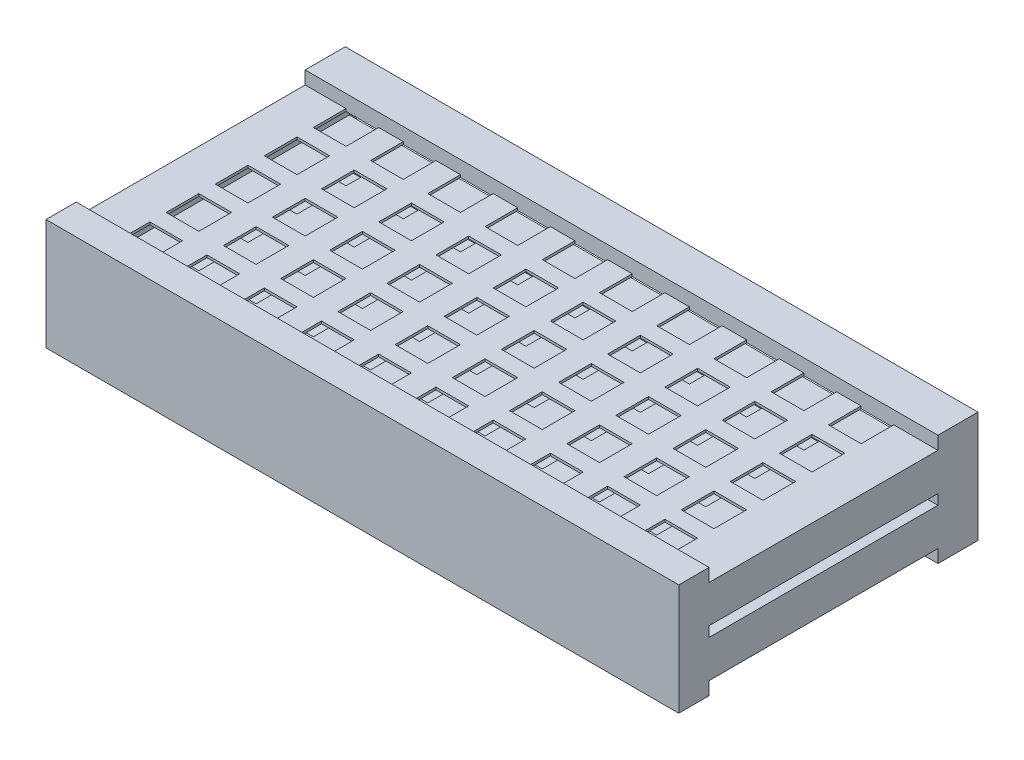
SolidWorks part; units mm, degrees
material "ABS"
ref_plane "Płaszczyzna przednia" through (0, 0, 0) normal (0, 0, 1) x (1, 0, 0)
ref_plane "Płaszczyzna górna" through (0, 0, 0) normal (0, 1, 0) x (1, 0, 0)
ref_plane "Płaszczyzna prawa" through (0, 0, 0) normal (1, 0, 0) x (0, 0, -1)
sketch "Szkic1" plane through (0, 0, 0) normal (0, 0, 1) x (1, 0, 0)
  line L15 (186, 34.1) -> (-188, 34.1)
  line L16 (186, 34.1) -> (186, -18.9)
  line L17 (186, -18.9) -> (-188, -18.9)
  line L18 (-188, 34.1) -> (-188, -18.9)
  point P0 (0, 0)
  dimension "D3" = 374
  dimension "D6" = 53
extrude "Dodanie-wyciągnięcie1" add sketch "Szkic1" along normal blind 177 contours L17 L18 L15 L16
sketch "Szkic5" plane through (0, -18.9, 0) normal (0, -1, 0) x (1, 0, 0)
  line L0 (186, 0) -> (-188, 0) construction
  line L1 (165.5, 48.5) -> (145.5, 48.5)
  line L2 (186, 177) -> (186, 0) construction
  line L3 (165.5, 48.5) -> (165.5, 68.5)
  line L4 (165.5, 68.5) -> (145.5, 68.5)
  line L5 (165.5, 18.5) -> (145.5, 18.5)
  line L6 (165.5, 18.5) -> (165.5, 38.5)
  line L7 (165.5, 38.5) -> (145.5, 38.5)
  line L8 (145.5, 18.5) -> (145.5, 38.5)
  line L9 (145.5, 48.5) -> (145.5, 68.5)
  line L10 (165.5, 78.5) -> (145.5, 78.5)
  line L11 (165.5, 78.5) -> (165.5, 98.5)
  line L12 (165.5, 98.5) -> (145.5, 98.5)
  line L13 (145.5, 78.5) -> (145.5, 98.5)
  line L14 (165.5, 108.5) -> (145.5, 108.5)
  line L15 (165.5, 108.5) -> (165.5, 128.5)
  line L16 (165.5, 128.5) -> (145.5, 128.5)
  line L17 (145.5, 108.5) -> (145.5, 128.5)
  line L18 (165.5, 138.5) -> (145.5, 138.5)
  line L19 (165.5, 138.5) -> (165.5, 158.5)
  line L20 (165.5, 158.5) -> (145.5, 158.5)
  line L21 (145.5, 138.5) -> (145.5, 158.5)
  line L22 (130.5, 48.5) -> (110.5, 48.5)
  line L23 (130.5, 48.5) -> (130.5, 68.5)
  line L24 (130.5, 68.5) -> (110.5, 68.5)
  line L25 (130.5, 18.5) -> (110.5, 18.5)
  line L26 (130.5, 18.5) -> (130.5, 38.5)
  line L27 (130.5, 38.5) -> (110.5, 38.5)
  line L28 (110.5, 18.5) -> (110.5, 38.5)
  line L29 (110.5, 48.5) -> (110.5, 68.5)
  line L30 (130.5, 78.5) -> (110.5, 78.5)
  line L31 (130.5, 78.5) -> (130.5, 98.5)
  line L32 (130.5, 98.5) -> (110.5, 98.5)
  line L33 (110.5, 78.5) -> (110.5, 98.5)
  line L34 (130.5, 108.5) -> (110.5, 108.5)
  line L35 (130.5, 108.5) -> (130.5, 128.5)
  line L36 (130.5, 128.5) -> (110.5, 128.5)
  line L37 (110.5, 108.5) -> (110.5, 128.5)
  line L38 (130.5, 138.5) -> (110.5, 138.5)
  line L39 (130.5, 138.5) -> (130.5, 158.5)
  line L40 (130.5, 158.5) -> (110.5, 158.5)
  line L41 (110.5, 138.5) -> (110.5, 158.5)
  line L42 (95.5, 48.5) -> (75.5, 48.5)
  line L43 (95.5, 48.5) -> (95.5, 68.5)
  line L44 (95.5, 68.5) -> (75.5, 68.5)
  line L45 (95.5, 18.5) -> (75.5, 18.5)
  line L46 (95.5, 18.5) -> (95.5, 38.5)
  line L47 (95.5, 38.5) -> (75.5, 38.5)
  line L48 (75.5, 18.5) -> (75.5, 38.5)
  line L49 (75.5, 48.5) -> (75.5, 68.5)
  line L50 (95.5, 78.5) -> (75.5, 78.5)
  line L51 (95.5, 78.5) -> (95.5, 98.5)
  line L52 (95.5, 98.5) -> (75.5, 98.5)
  line L53 (75.5, 78.5) -> (75.5, 98.5)
  line L54 (95.5, 108.5) -> (75.5, 108.5)
  line L55 (95.5, 108.5) -> (95.5, 128.5)
  line L56 (95.5, 128.5) -> (75.5, 128.5)
  line L57 (75.5, 108.5) -> (75.5, 128.5)
  line L58 (95.5, 138.5) -> (75.5, 138.5)
  line L59 (95.5, 138.5) -> (95.5, 158.5)
  line L60 (95.5, 158.5) -> (75.5, 158.5)
  line L61 (75.5, 138.5) -> (75.5, 158.5)
  line L62 (60.5, 48.5) -> (40.5, 48.5)
  line L63 (60.5, 48.5) -> (60.5, 68.5)
  line L64 (60.5, 68.5) -> (40.5, 68.5)
  line L65 (60.5, 18.5) -> (40.5, 18.5)
  line L66 (60.5, 18.5) -> (60.5, 38.5)
  line L67 (60.5, 38.5) -> (40.5, 38.5)
  line L68 (40.5, 18.5) -> (40.5, 38.5)
  line L69 (40.5, 48.5) -> (40.5, 68.5)
  line L70 (60.5, 78.5) -> (40.5, 78.5)
  line L71 (60.5, 78.5) -> (60.5, 98.5)
  line L72 (60.5, 98.5) -> (40.5, 98.5)
  line L73 (40.5, 78.5) -> (40.5, 98.5)
  line L74 (60.5, 108.5) -> (40.5, 108.5)
  line L75 (60.5, 108.5) -> (60.5, 128.5)
  line L76 (60.5, 128.5) -> (40.5, 128.5)
  line L77 (40.5, 108.5) -> (40.5, 128.5)
  line L78 (60.5, 138.5) -> (40.5, 138.5)
  line L79 (60.5, 138.5) -> (60.5, 158.5)
  line L80 (60.5, 158.5) -> (40.5, 158.5)
  line L81 (40.5, 138.5) -> (40.5, 158.5)
  line L82 (25.5, 48.5) -> (5.5, 48.5)
  line L83 (25.5, 48.5) -> (25.5, 68.5)
  line L84 (25.5, 68.5) -> (5.5, 68.5)
  line L85 (25.5, 18.5) -> (5.5, 18.5)
  line L86 (25.5, 18.5) -> (25.5, 38.5)
  line L87 (25.5, 38.5) -> (5.5, 38.5)
  line L88 (5.5, 18.5) -> (5.5, 38.5)
  line L89 (5.5, 48.5) -> (5.5, 68.5)
  line L90 (25.5, 78.5) -> (5.5, 78.5)
  line L91 (25.5, 78.5) -> (25.5, 98.5)
  line L92 (25.5, 98.5) -> (5.5, 98.5)
  line L93 (5.5, 78.5) -> (5.5, 98.5)
  line L94 (25.5, 108.5) -> (5.5, 108.5)
  line L95 (25.5, 108.5) -> (25.5, 128.5)
  line L96 (25.5, 128.5) -> (5.5, 128.5)
  line L97 (5.5, 108.5) -> (5.5, 128.5)
  line L98 (25.5, 138.5) -> (5.5, 138.5)
  line L99 (25.5, 138.5) -> (25.5, 158.5)
  line L100 (25.5, 158.5) -> (5.5, 158.5)
  line L101 (5.5, 138.5) -> (5.5, 158.5)
  line L102 (-9.5, 48.5) -> (-29.5, 48.5)
  line L103 (-9.5, 48.5) -> (-9.5, 68.5)
  line L104 (-9.5, 68.5) -> (-29.5, 68.5)
  line L105 (-9.5, 18.5) -> (-29.5, 18.5)
  line L106 (-9.5, 18.5) -> (-9.5, 38.5)
  line L107 (-9.5, 38.5) -> (-29.5, 38.5)
  line L108 (-29.5, 18.5) -> (-29.5, 38.5)
  line L109 (-29.5, 48.5) -> (-29.5, 68.5)
  line L110 (-9.5, 78.5) -> (-29.5, 78.5)
  line L111 (-9.5, 78.5) -> (-9.5, 98.5)
  line L112 (-9.5, 98.5) -> (-29.5, 98.5)
  line L113 (-29.5, 78.5) -> (-29.5, 98.5)
  line L114 (-9.5, 108.5) -> (-29.5, 108.5)
  line L115 (-9.5, 108.5) -> (-9.5, 128.5)
  line L116 (-9.5, 128.5) -> (-29.5, 128.5)
  line L117 (-29.5, 108.5) -> (-29.5, 128.5)
  line L118 (-9.5, 138.5) -> (-29.5, 138.5)
  line L119 (-9.5, 138.5) -> (-9.5, 158.5)
  line L120 (-9.5, 158.5) -> (-29.5, 158.5)
  line L121 (-29.5, 138.5) -> (-29.5, 158.5)
  line L122 (-44.5, 48.5) -> (-64.5, 48.5)
  line L123 (-44.5, 48.5) -> (-44.5, 68.5)
  line L124 (-44.5, 68.5) -> (-64.5, 68.5)
  line L125 (-44.5, 18.5) -> (-64.5, 18.5)
  line L126 (-44.5, 18.5) -> (-44.5, 38.5)
  line L127 (-44.5, 38.5) -> (-64.5, 38.5)
  line L128 (-64.5, 18.5) -> (-64.5, 38.5)
  line L129 (-64.5, 48.5) -> (-64.5, 68.5)
  line L130 (-44.5, 78.5) -> (-64.5, 78.5)
  line L131 (-44.5, 78.5) -> (-44.5, 98.5)
  line L132 (-44.5, 98.5) -> (-64.5, 98.5)
  line L133 (-64.5, 78.5) -> (-64.5, 98.5)
  line L134 (-44.5, 108.5) -> (-64.5, 108.5)
  line L135 (-44.5, 108.5) -> (-44.5, 128.5)
  line L136 (-44.5, 128.5) -> (-64.5, 128.5)
  line L137 (-64.5, 108.5) -> (-64.5, 128.5)
  line L138 (-44.5, 138.5) -> (-64.5, 138.5)
  line L139 (-44.5, 138.5) -> (-44.5, 158.5)
  line L140 (-44.5, 158.5) -> (-64.5, 158.5)
  line L141 (-64.5, 138.5) -> (-64.5, 158.5)
  line L142 (-79.5, 48.5) -> (-99.5, 48.5)
  line L143 (-79.5, 48.5) -> (-79.5, 68.5)
  line L144 (-79.5, 68.5) -> (-99.5, 68.5)
  line L145 (-79.5, 18.5) -> (-99.5, 18.5)
  line L146 (-79.5, 18.5) -> (-79.5, 38.5)
  line L147 (-79.5, 38.5) -> (-99.5, 38.5)
  line L148 (-99.5, 18.5) -> (-99.5, 38.5)
  line L149 (-99.5, 48.5) -> (-99.5, 68.5)
  line L150 (-79.5, 78.5) -> (-99.5, 78.5)
  line L151 (-79.5, 78.5) -> (-79.5, 98.5)
  line L152 (-79.5, 98.5) -> (-99.5, 98.5)
  line L153 (-99.5, 78.5) -> (-99.5, 98.5)
  line L154 (-79.5, 108.5) -> (-99.5, 108.5)
  line L155 (-79.5, 108.5) -> (-79.5, 128.5)
  line L156 (-79.5, 128.5) -> (-99.5, 128.5)
  line L157 (-99.5, 108.5) -> (-99.5, 128.5)
  line L158 (-79.5, 138.5) -> (-99.5, 138.5)
  line L159 (-79.5, 138.5) -> (-79.5, 158.5)
  line L160 (-79.5, 158.5) -> (-99.5, 158.5)
  line L161 (-99.5, 138.5) -> (-99.5, 158.5)
  line L162 (-114.5, 48.5) -> (-134.5, 48.5)
  line L163 (-114.5, 48.5) -> (-114.5, 68.5)
  line L164 (-114.5, 68.5) -> (-134.5, 68.5)
  line L165 (-114.5, 18.5) -> (-134.5, 18.5)
  line L166 (-114.5, 18.5) -> (-114.5, 38.5)
  line L167 (-114.5, 38.5) -> (-134.5, 38.5)
  line L168 (-134.5, 18.5) -> (-134.5, 38.5)
  line L169 (-134.5, 48.5) -> (-134.5, 68.5)
  line L170 (-114.5, 78.5) -> (-134.5, 78.5)
  line L171 (-114.5, 78.5) -> (-114.5, 98.5)
  line L172 (-114.5, 98.5) -> (-134.5, 98.5)
  line L173 (-134.5, 78.5) -> (-134.5, 98.5)
  line L174 (-114.5, 108.5) -> (-134.5, 108.5)
  line L175 (-114.5, 108.5) -> (-114.5, 128.5)
  line L176 (-114.5, 128.5) -> (-134.5, 128.5)
  line L177 (-134.5, 108.5) -> (-134.5, 128.5)
  line L178 (-114.5, 138.5) -> (-134.5, 138.5)
  line L179 (-114.5, 138.5) -> (-114.5, 158.5)
  line L180 (-114.5, 158.5) -> (-134.5, 158.5)
  line L181 (-134.5, 138.5) -> (-134.5, 158.5)
  line L182 (-149.5, 48.5) -> (-169.5, 48.5)
  line L183 (-149.5, 48.5) -> (-149.5, 68.5)
  line L184 (-149.5, 68.5) -> (-169.5, 68.5)
  line L185 (-149.5, 18.5) -> (-169.5, 18.5)
  line L186 (-149.5, 18.5) -> (-149.5, 38.5)
  line L187 (-149.5, 38.5) -> (-169.5, 38.5)
  line L188 (-169.5, 18.5) -> (-169.5, 38.5)
  line L189 (-169.5, 48.5) -> (-169.5, 68.5)
  line L190 (-149.5, 78.5) -> (-169.5, 78.5)
  line L191 (-149.5, 78.5) -> (-149.5, 98.5)
  line L192 (-149.5, 98.5) -> (-169.5, 98.5)
  line L193 (-169.5, 78.5) -> (-169.5, 98.5)
  line L194 (-149.5, 108.5) -> (-169.5, 108.5)
  line L195 (-149.5, 108.5) -> (-149.5, 128.5)
  line L196 (-149.5, 128.5) -> (-169.5, 128.5)
  line L197 (-169.5, 108.5) -> (-169.5, 128.5)
  line L198 (-149.5, 138.5) -> (-169.5, 138.5)
  line L199 (-149.5, 138.5) -> (-149.5, 158.5)
  line L200 (-149.5, 158.5) -> (-169.5, 158.5)
  line L201 (-169.5, 138.5) -> (-169.5, 158.5)
  line L202 (186, 177) -> (-188, 177) construction
  line L203 (-188, 177) -> (-188, 0) construction
  dimension "D1" = 18.5
  dimension "D2" = 20.5
  dimension "D3" = 20
  dimension "D4" = 20
  dimension "D7" = 20
  dimension "D8" = 20
  dimension "D9" = 15
  dimension "D10" = 18.5
  dimension "D11" = 18.5
  dimension "D5" = 5
  dimension "D6" = 10
extrude "Wytnij-wyciągnięcie4" cut sketch "Szkic5" against normal blind 104
sketch "Szkic7" plane through (0, 0, 0) normal (0, 0, -1) x (-1, 0, 0)
  line L5 (-186, -18.9) -> (188, -18.9) construction
  line L7 (-184, 32.1) -> (186, 32.1)
  line L8 (-184, 32.1) -> (-184, 12.7)
  line L9 (-184, 12.7) -> (186, 12.7)
  line L10 (186, 32.1) -> (186, 12.7)
  line L12 (-186, 34.1) -> (-186, -18.9) construction
  line L13 (-184, -16.9) -> (186, -16.9)
  line L14 (-184, -16.9) -> (-184, 2.5)
  line L15 (-184, 2.5) -> (186, 2.5)
  line L16 (186, -16.9) -> (186, 2.5)
  line L17 (-186, 34.1) -> (188, 34.1) construction
  dimension "D1" = 370
  dimension "D2" = 2
  dimension "D3" = 2
  dimension "D4" = 2
  dimension "D5" = 2
  dimension "D6" = 370
  dimension "D7" = 370
  dimension "D8" = 19.4
  dimension "D9" = 19.4
extrude "Wytnij-wyciągnięcie5" cut sketch "Szkic7" against normal blind 175
sketch "Szkic9" plane through (186, 0, 0) normal (1, 0, 0) x (0, 0, -1)
  line L15 (-158.5, 10.7) -> (-158.5, 4.5)
  line L17 (-18.5, 10.7) -> (-158.5, 10.7)
  line L18 (-18.5, 10.7) -> (-18.5, 4.5)
  line L19 (-18.5, 4.5) -> (-158.5, 4.5)
extrude "Wytnij-wyciągnięcie6" cut sketch "Szkic9" against normal blind 374
sketch "Szkic15" plane through (0, 34.1, 0) normal (0, 1, 0) x (1, 0, 0)
  line L1 (-188, 0) -> (186, 0)
  line L2 (-188, 0) -> (-188, -177)
  line L3 (-188, -177) -> (186, -177)
  line L4 (186, 0) -> (186, -177)
  line L5 (-169.5, -18.5) -> (-149.5, -18.5)
  line L6 (-169.5, -18.5) -> (-169.5, -38.5)
  line L7 (-169.5, -38.5) -> (-149.5, -38.5)
  line L8 (-149.5, -18.5) -> (-149.5, -38.5)
  line L9 (-134.5, -18.5) -> (-114.5, -18.5)
  line L10 (-134.5, -18.5) -> (-134.5, -38.5)
  line L11 (-134.5, -38.5) -> (-114.5, -38.5)
  line L12 (-114.5, -18.5) -> (-114.5, -38.5)
  line L13 (-99.5, -18.5) -> (-79.5, -18.5)
  line L14 (-99.5, -18.5) -> (-99.5, -38.5)
  line L15 (-99.5, -38.5) -> (-79.5, -38.5)
  line L16 (-79.5, -18.5) -> (-79.5, -38.5)
  line L17 (-64.5, -18.5) -> (-44.5, -18.5)
  line L18 (-64.5, -18.5) -> (-64.5, -38.5)
  line L19 (-64.5, -38.5) -> (-44.5, -38.5)
  line L20 (-44.5, -18.5) -> (-44.5, -38.5)
  line L21 (-29.5, -18.5) -> (-9.5, -18.5)
  line L22 (-29.5, -18.5) -> (-29.5, -38.5)
  line L23 (-29.5, -38.5) -> (-9.5, -38.5)
  line L24 (-9.5, -18.5) -> (-9.5, -38.5)
  line L25 (5.5, -18.5) -> (25.5, -18.5)
  line L26 (5.5, -18.5) -> (5.5, -38.5)
  line L27 (5.5, -38.5) -> (25.5, -38.5)
  line L28 (25.5, -18.5) -> (25.5, -38.5)
  line L29 (40.5, -18.5) -> (60.5, -18.5)
  line L30 (40.5, -18.5) -> (40.5, -38.5)
  line L31 (40.5, -38.5) -> (60.5, -38.5)
  line L32 (60.5, -18.5) -> (60.5, -38.5)
  line L33 (75.5, -18.5) -> (95.5, -18.5)
  line L34 (75.5, -18.5) -> (75.5, -38.5)
  line L35 (75.5, -38.5) -> (95.5, -38.5)
  line L36 (95.5, -18.5) -> (95.5, -38.5)
  line L37 (110.5, -18.5) -> (130.5, -18.5)
  line L38 (110.5, -18.5) -> (110.5, -38.5)
  line L39 (110.5, -38.5) -> (130.5, -38.5)
  line L40 (130.5, -18.5) -> (130.5, -38.5)
  line L41 (145.5, -18.5) -> (165.5, -18.5)
  line L42 (145.5, -18.5) -> (145.5, -38.5)
  line L43 (145.5, -38.5) -> (165.5, -38.5)
  line L44 (165.5, -18.5) -> (165.5, -38.5)
  line L45 (145.5, -48.5) -> (165.5, -48.5)
  line L46 (145.5, -48.5) -> (145.5, -68.5)
  line L47 (145.5, -68.5) -> (165.5, -68.5)
  line L48 (165.5, -48.5) -> (165.5, -68.5)
  line L49 (145.5, -78.5) -> (165.5, -78.5)
  line L50 (145.5, -78.5) -> (145.5, -98.5)
  line L51 (145.5, -98.5) -> (165.5, -98.5)
  line L52 (165.5, -78.5) -> (165.5, -98.5)
  line L53 (145.5, -108.5) -> (165.5, -108.5)
  line L54 (145.5, -108.5) -> (145.5, -128.5)
  line L55 (145.5, -128.5) -> (165.5, -128.5)
  line L56 (165.5, -108.5) -> (165.5, -128.5)
  line L57 (145.5, -138.5) -> (165.5, -138.5)
  line L58 (145.5, -138.5) -> (145.5, -158.5)
  line L59 (145.5, -158.5) -> (165.5, -158.5)
  line L60 (165.5, -138.5) -> (165.5, -158.5)
  line L61 (110.5, -48.5) -> (130.5, -48.5)
  line L62 (110.5, -48.5) -> (110.5, -68.5)
  line L63 (110.5, -68.5) -> (130.5, -68.5)
  line L64 (130.5, -48.5) -> (130.5, -68.5)
  line L65 (110.5, -78.5) -> (130.5, -78.5)
  line L66 (110.5, -78.5) -> (110.5, -98.5)
  line L67 (110.5, -98.5) -> (130.5, -98.5)
  line L68 (130.5, -78.5) -> (130.5, -98.5)
  line L69 (110.5, -108.5) -> (130.5, -108.5)
  line L70 (110.5, -108.5) -> (110.5, -128.5)
  line L71 (110.5, -128.5) -> (130.5, -128.5)
  line L72 (130.5, -108.5) -> (130.5, -128.5)
  line L73 (110.5, -138.5) -> (130.5, -138.5)
  line L74 (110.5, -138.5) -> (110.5, -158.5)
  line L75 (110.5, -158.5) -> (130.5, -158.5)
  line L76 (130.5, -138.5) -> (130.5, -158.5)
  line L77 (75.5, -48.5) -> (95.5, -48.5)
  line L78 (75.5, -48.5) -> (75.5, -68.5)
  line L79 (75.5, -68.5) -> (95.5, -68.5)
  line L80 (95.5, -48.5) -> (95.5, -68.5)
  line L81 (75.5, -78.5) -> (95.5, -78.5)
  line L82 (75.5, -78.5) -> (75.5, -98.5)
  line L83 (75.5, -98.5) -> (95.5, -98.5)
  line L84 (95.5, -78.5) -> (95.5, -98.5)
  line L85 (75.5, -108.5) -> (95.5, -108.5)
  line L86 (75.5, -108.5) -> (75.5, -128.5)
  line L87 (75.5, -128.5) -> (95.5, -128.5)
  line L88 (95.5, -108.5) -> (95.5, -128.5)
  line L89 (75.5, -138.5) -> (95.5, -138.5)
  line L90 (75.5, -138.5) -> (75.5, -158.5)
  line L91 (75.5, -158.5) -> (95.5, -158.5)
  line L92 (95.5, -138.5) -> (95.5, -158.5)
  line L93 (40.5, -48.5) -> (60.5, -48.5)
  line L94 (40.5, -48.5) -> (40.5, -68.5)
  line L95 (40.5, -68.5) -> (60.5, -68.5)
  line L96 (60.5, -48.5) -> (60.5, -68.5)
  line L97 (40.5, -78.5) -> (60.5, -78.5)
  line L98 (40.5, -78.5) -> (40.5, -98.5)
  line L99 (40.5, -98.5) -> (60.5, -98.5)
  line L100 (60.5, -78.5) -> (60.5, -98.5)
  line L101 (40.5, -108.5) -> (60.5, -108.5)
  line L102 (40.5, -108.5) -> (40.5, -128.5)
  line L103 (40.5, -128.5) -> (60.5, -128.5)
  line L104 (60.5, -108.5) -> (60.5, -128.5)
  line L105 (5.5, -48.5) -> (25.5, -48.5)
  line L106 (5.5, -48.5) -> (5.5, -68.5)
  line L107 (5.5, -68.5) -> (25.5, -68.5)
  line L108 (25.5, -48.5) -> (25.5, -68.5)
  line L109 (5.5, -78.5) -> (25.5, -78.5)
  line L110 (5.5, -78.5) -> (5.5, -98.5)
  line L111 (5.5, -98.5) -> (25.5, -98.5)
  line L112 (25.5, -78.5) -> (25.5, -98.5)
  line L113 (5.5, -108.5) -> (25.5, -108.5)
  line L114 (5.5, -108.5) -> (5.5, -128.5)
  line L115 (5.5, -128.5) -> (25.5, -128.5)
  line L116 (25.5, -108.5) -> (25.5, -128.5)
  line L117 (5.5, -138.5) -> (25.5, -138.5)
  line L118 (5.5, -138.5) -> (5.5, -158.5)
  line L119 (5.5, -158.5) -> (25.5, -158.5)
  line L120 (25.5, -138.5) -> (25.5, -158.5)
  line L121 (40.5, -138.5) -> (60.5, -138.5)
  line L122 (40.5, -138.5) -> (40.5, -158.5)
  line L123 (40.5, -158.5) -> (60.5, -158.5)
  line L124 (60.5, -138.5) -> (60.5, -158.5)
  line L125 (-29.5, -48.5) -> (-9.5, -48.5)
  line L126 (-29.5, -48.5) -> (-29.5, -68.5)
  line L127 (-29.5, -68.5) -> (-9.5, -68.5)
  line L128 (-9.5, -48.5) -> (-9.5, -68.5)
  line L129 (-29.5, -78.5) -> (-9.5, -78.5)
  line L130 (-29.5, -78.5) -> (-29.5, -98.5)
  line L131 (-29.5, -98.5) -> (-9.5, -98.5)
  line L132 (-9.5, -78.5) -> (-9.5, -98.5)
  line L133 (-29.5, -108.5) -> (-9.5, -108.5)
  line L134 (-29.5, -108.5) -> (-29.5, -128.5)
  line L135 (-29.5, -128.5) -> (-9.5, -128.5)
  line L136 (-9.5, -108.5) -> (-9.5, -128.5)
  line L137 (-29.5, -138.5) -> (-9.5, -138.5)
  line L138 (-29.5, -138.5) -> (-29.5, -158.5)
  line L139 (-29.5, -158.5) -> (-9.5, -158.5)
  line L140 (-9.5, -138.5) -> (-9.5, -158.5)
  line L141 (-64.5, -48.5) -> (-44.5, -48.5)
  line L142 (-64.5, -48.5) -> (-64.5, -68.5)
  line L143 (-64.5, -68.5) -> (-44.5, -68.5)
  line L144 (-44.5, -48.5) -> (-44.5, -68.5)
  line L145 (-64.5, -78.5) -> (-44.5, -78.5)
  line L146 (-64.5, -78.5) -> (-64.5, -98.5)
  line L147 (-64.5, -98.5) -> (-44.5, -98.5)
  line L148 (-44.5, -78.5) -> (-44.5, -98.5)
  line L149 (-64.5, -108.5) -> (-44.5, -108.5)
  line L150 (-64.5, -108.5) -> (-64.5, -128.5)
  line L151 (-64.5, -128.5) -> (-44.5, -128.5)
  line L152 (-44.5, -108.5) -> (-44.5, -128.5)
  line L153 (-64.5, -138.5) -> (-44.5, -138.5)
  line L154 (-64.5, -138.5) -> (-64.5, -158.5)
  line L155 (-64.5, -158.5) -> (-44.5, -158.5)
  line L156 (-44.5, -138.5) -> (-44.5, -158.5)
  line L157 (-99.5, -48.5) -> (-79.5, -48.5)
  line L158 (-99.5, -48.5) -> (-99.5, -68.5)
  line L159 (-99.5, -68.5) -> (-79.5, -68.5)
  line L160 (-79.5, -48.5) -> (-79.5, -68.5)
  line L161 (-99.5, -78.5) -> (-79.5, -78.5)
  line L162 (-99.5, -78.5) -> (-99.5, -98.5)
  line L163 (-99.5, -98.5) -> (-79.5, -98.5)
  line L164 (-79.5, -78.5) -> (-79.5, -98.5)
  line L165 (-99.5, -108.5) -> (-79.5, -108.5)
  line L166 (-99.5, -108.5) -> (-99.5, -128.5)
  line L167 (-99.5, -128.5) -> (-79.5, -128.5)
  line L168 (-79.5, -108.5) -> (-79.5, -128.5)
  line L169 (-99.5, -138.5) -> (-79.5, -138.5)
  line L170 (-99.5, -138.5) -> (-99.5, -158.5)
  line L171 (-99.5, -158.5) -> (-79.5, -158.5)
  line L172 (-79.5, -138.5) -> (-79.5, -158.5)
  line L173 (-134.5, -48.5) -> (-114.5, -48.5)
  line L174 (-134.5, -48.5) -> (-134.5, -68.5)
  line L175 (-134.5, -68.5) -> (-114.5, -68.5)
  line L176 (-114.5, -48.5) -> (-114.5, -68.5)
  line L177 (-134.5, -78.5) -> (-114.5, -78.5)
  line L178 (-134.5, -78.5) -> (-134.5, -98.5)
  line L179 (-134.5, -98.5) -> (-114.5, -98.5)
  line L180 (-114.5, -78.5) -> (-114.5, -98.5)
  line L181 (-134.5, -108.5) -> (-114.5, -108.5)
  line L182 (-134.5, -108.5) -> (-134.5, -128.5)
  line L183 (-134.5, -128.5) -> (-114.5, -128.5)
  line L184 (-114.5, -108.5) -> (-114.5, -128.5)
  line L185 (-134.5, -138.5) -> (-114.5, -138.5)
  line L186 (-134.5, -138.5) -> (-134.5, -158.5)
  line L187 (-134.5, -158.5) -> (-114.5, -158.5)
  line L188 (-114.5, -138.5) -> (-114.5, -158.5)
  line L189 (-169.5, -48.5) -> (-149.5, -48.5)
  line L190 (-169.5, -48.5) -> (-169.5, -68.5)
  line L191 (-169.5, -68.5) -> (-149.5, -68.5)
  line L192 (-149.5, -48.5) -> (-149.5, -68.5)
  line L193 (-169.5, -78.5) -> (-149.5, -78.5)
  line L194 (-169.5, -78.5) -> (-169.5, -98.5)
  line L195 (-169.5, -98.5) -> (-149.5, -98.5)
  line L196 (-149.5, -78.5) -> (-149.5, -98.5)
  line L197 (-169.5, -108.5) -> (-149.5, -108.5)
  line L198 (-169.5, -108.5) -> (-169.5, -128.5)
  line L199 (-169.5, -128.5) -> (-149.5, -128.5)
  line L200 (-149.5, -108.5) -> (-149.5, -128.5)
  line L201 (-169.5, -138.5) -> (-149.5, -138.5)
  line L202 (-169.5, -138.5) -> (-169.5, -158.5)
  line L203 (-169.5, -158.5) -> (-149.5, -158.5)
  line L204 (-149.5, -138.5) -> (-149.5, -158.5)
extrude "Dodanie-wyciągnięcie6" add sketch "Szkic15" along normal blind 1
sketch "Szkic16" plane through (0, -18.9, 0) normal (0, -1, 0) x (1, 0, 0)
  line L1 (186, 0) -> (-188, 0)
  line L2 (186, 0) -> (186, 177)
  line L3 (186, 177) -> (-188, 177)
  line L4 (-188, 0) -> (-188, 177)
  line L5 (165.5, 18.5) -> (145.5, 18.5)
  line L6 (165.5, 18.5) -> (165.5, 38.5)
  line L7 (165.5, 38.5) -> (145.5, 38.5)
  line L8 (145.5, 18.5) -> (145.5, 38.5)
  line L9 (130.5, 18.5) -> (110.5, 18.5)
  line L10 (130.5, 18.5) -> (130.5, 38.5)
  line L11 (130.5, 38.5) -> (110.5, 38.5)
  line L12 (110.5, 18.5) -> (110.5, 38.5)
  line L13 (95.5, 18.5) -> (75.5, 18.5)
  line L14 (95.5, 18.5) -> (95.5, 38.5)
  line L15 (95.5, 38.5) -> (75.5, 38.5)
  line L16 (75.5, 18.5) -> (75.5, 38.5)
  line L17 (60.5, 18.5) -> (40.5, 18.5)
  line L18 (60.5, 18.5) -> (60.5, 38.5)
  line L19 (60.5, 38.5) -> (40.5, 38.5)
  line L20 (40.5, 18.5) -> (40.5, 38.5)
  line L21 (25.5, 18.5) -> (5.5, 18.5)
  line L22 (25.5, 18.5) -> (25.5, 38.5)
  line L23 (25.5, 38.5) -> (5.5, 38.5)
  line L24 (5.5, 18.5) -> (5.5, 38.5)
  line L25 (-9.5, 18.5) -> (-29.5, 18.5)
  line L26 (-9.5, 18.5) -> (-9.5, 38.5)
  line L27 (-9.5, 38.5) -> (-29.5, 38.5)
  line L28 (-29.5, 18.5) -> (-29.5, 38.5)
  line L29 (-44.5, 18.5) -> (-64.5, 18.5)
  line L30 (-44.5, 18.5) -> (-44.5, 38.5)
  line L31 (-44.5, 38.5) -> (-64.5, 38.5)
  line L32 (-64.5, 18.5) -> (-64.5, 38.5)
  line L33 (-79.5, 18.5) -> (-99.5, 18.5)
  line L34 (-79.5, 18.5) -> (-79.5, 38.5)
  line L35 (-79.5, 38.5) -> (-99.5, 38.5)
  line L36 (-99.5, 18.5) -> (-99.5, 38.5)
  line L37 (-114.5, 18.5) -> (-134.5, 18.5)
  line L38 (-114.5, 18.5) -> (-114.5, 38.5)
  line L39 (-114.5, 38.5) -> (-134.5, 38.5)
  line L40 (-134.5, 18.5) -> (-134.5, 38.5)
  line L41 (-149.5, 18.5) -> (-169.5, 18.5)
  line L42 (-149.5, 18.5) -> (-149.5, 38.5)
  line L43 (-149.5, 38.5) -> (-169.5, 38.5)
  line L44 (-169.5, 18.5) -> (-169.5, 38.5)
  line L45 (165.5, 48.5) -> (145.5, 48.5)
  line L46 (165.5, 48.5) -> (165.5, 68.5)
  line L47 (165.5, 68.5) -> (145.5, 68.5)
  line L48 (145.5, 48.5) -> (145.5, 68.5)
  line L49 (130.5, 48.5) -> (110.5, 48.5)
  line L50 (130.5, 48.5) -> (130.5, 68.5)
  line L51 (130.5, 68.5) -> (110.5, 68.5)
  line L52 (110.5, 48.5) -> (110.5, 68.5)
  line L53 (95.5, 48.5) -> (75.5, 48.5)
  line L54 (95.5, 48.5) -> (95.5, 68.5)
  line L55 (95.5, 68.5) -> (75.5, 68.5)
  line L56 (75.5, 48.5) -> (75.5, 68.5)
  line L57 (60.5, 48.5) -> (40.5, 48.5)
  line L58 (60.5, 48.5) -> (60.5, 68.5)
  line L59 (60.5, 68.5) -> (40.5, 68.5)
  line L60 (40.5, 48.5) -> (40.5, 68.5)
  line L61 (25.5, 48.5) -> (5.5, 48.5)
  line L62 (25.5, 48.5) -> (25.5, 68.5)
  line L63 (25.5, 68.5) -> (5.5, 68.5)
  line L64 (5.5, 48.5) -> (5.5, 68.5)
  line L65 (-9.5, 48.5) -> (-29.5, 48.5)
  line L66 (-9.5, 48.5) -> (-9.5, 68.5)
  line L67 (-9.5, 68.5) -> (-29.5, 68.5)
  line L68 (-29.5, 48.5) -> (-29.5, 68.5)
  line L69 (-44.5, 48.5) -> (-64.5, 48.5)
  line L70 (-44.5, 48.5) -> (-44.5, 68.5)
  line L71 (-44.5, 68.5) -> (-64.5, 68.5)
  line L72 (-64.5, 48.5) -> (-64.5, 68.5)
  line L73 (-79.5, 48.5) -> (-99.5, 48.5)
  line L74 (-79.5, 48.5) -> (-79.5, 68.5)
  line L75 (-79.5, 68.5) -> (-99.5, 68.5)
  line L76 (-99.5, 48.5) -> (-99.5, 68.5)
  line L77 (-114.5, 48.5) -> (-134.5, 48.5)
  line L78 (-114.5, 48.5) -> (-114.5, 68.5)
  line L79 (-114.5, 68.5) -> (-134.5, 68.5)
  line L80 (-134.5, 48.5) -> (-134.5, 68.5)
  line L81 (-149.5, 48.5) -> (-169.5, 48.5)
  line L82 (-149.5, 48.5) -> (-149.5, 68.5)
  line L83 (-149.5, 68.5) -> (-169.5, 68.5)
  line L84 (-169.5, 48.5) -> (-169.5, 68.5)
  line L85 (-149.5, 78.5) -> (-169.5, 78.5)
  line L86 (-149.5, 78.5) -> (-149.5, 98.5)
  line L87 (-149.5, 98.5) -> (-169.5, 98.5)
  line L88 (-169.5, 78.5) -> (-169.5, 98.5)
  line L89 (-149.5, 108.5) -> (-169.5, 108.5)
  line L90 (-149.5, 108.5) -> (-149.5, 128.5)
  line L91 (-149.5, 128.5) -> (-169.5, 128.5)
  line L92 (-169.5, 108.5) -> (-169.5, 128.5)
  line L93 (-149.5, 138.5) -> (-169.5, 138.5)
  line L94 (-149.5, 138.5) -> (-149.5, 158.5)
  line L95 (-149.5, 158.5) -> (-169.5, 158.5)
  line L96 (-169.5, 138.5) -> (-169.5, 158.5)
  line L97 (-114.5, 78.5) -> (-134.5, 78.5)
  line L98 (-114.5, 78.5) -> (-114.5, 98.5)
  line L99 (-114.5, 98.5) -> (-134.5, 98.5)
  line L100 (-134.5, 78.5) -> (-134.5, 98.5)
  line L101 (-114.5, 108.5) -> (-134.5, 108.5)
  line L102 (-114.5, 108.5) -> (-114.5, 128.5)
  line L103 (-114.5, 128.5) -> (-134.5, 128.5)
  line L104 (-134.5, 108.5) -> (-134.5, 128.5)
  line L105 (-114.5, 138.5) -> (-134.5, 138.5)
  line L106 (-114.5, 138.5) -> (-114.5, 158.5)
  line L107 (-114.5, 158.5) -> (-134.5, 158.5)
  line L108 (-134.5, 138.5) -> (-134.5, 158.5)
  line L109 (-79.5, 78.5) -> (-99.5, 78.5)
  line L110 (-79.5, 78.5) -> (-79.5, 98.5)
  line L111 (-79.5, 98.5) -> (-99.5, 98.5)
  line L112 (-99.5, 78.5) -> (-99.5, 98.5)
  line L113 (-79.5, 108.5) -> (-99.5, 108.5)
  line L114 (-79.5, 108.5) -> (-79.5, 128.5)
  line L115 (-79.5, 128.5) -> (-99.5, 128.5)
  line L116 (-99.5, 108.5) -> (-99.5, 128.5)
  line L117 (-79.5, 138.5) -> (-99.5, 138.5)
  line L118 (-79.5, 138.5) -> (-79.5, 158.5)
  line L119 (-79.5, 158.5) -> (-99.5, 158.5)
  line L120 (-99.5, 138.5) -> (-99.5, 158.5)
  line L121 (-44.5, 78.5) -> (-64.5, 78.5)
  line L122 (-44.5, 78.5) -> (-44.5, 98.5)
  line L123 (-44.5, 98.5) -> (-64.5, 98.5)
  line L124 (-64.5, 78.5) -> (-64.5, 98.5)
  line L125 (-44.5, 108.5) -> (-64.5, 108.5)
  line L126 (-44.5, 108.5) -> (-44.5, 128.5)
  line L127 (-44.5, 128.5) -> (-64.5, 128.5)
  line L128 (-64.5, 108.5) -> (-64.5, 128.5)
  line L129 (-44.5, 138.5) -> (-64.5, 138.5)
  line L130 (-44.5, 138.5) -> (-44.5, 158.5)
  line L131 (-44.5, 158.5) -> (-64.5, 158.5)
  line L132 (-64.5, 138.5) -> (-64.5, 158.5)
  line L133 (-9.5, 78.5) -> (-29.5, 78.5)
  line L134 (-9.5, 78.5) -> (-9.5, 98.5)
  line L135 (-9.5, 98.5) -> (-29.5, 98.5)
  line L136 (-29.5, 78.5) -> (-29.5, 98.5)
  line L137 (-9.5, 108.5) -> (-29.5, 108.5)
  line L138 (-9.5, 108.5) -> (-9.5, 128.5)
  line L139 (-9.5, 128.5) -> (-29.5, 128.5)
  line L140 (-29.5, 108.5) -> (-29.5, 128.5)
  line L141 (-9.5, 138.5) -> (-29.5, 138.5)
  line L142 (-9.5, 138.5) -> (-9.5, 158.5)
  line L143 (-9.5, 158.5) -> (-29.5, 158.5)
  line L144 (-29.5, 138.5) -> (-29.5, 158.5)
  line L145 (25.5, 78.5) -> (5.5, 78.5)
  line L146 (25.5, 78.5) -> (25.5, 98.5)
  line L147 (25.5, 98.5) -> (5.5, 98.5)
  line L148 (5.5, 78.5) -> (5.5, 98.5)
  line L149 (25.5, 108.5) -> (5.5, 108.5)
  line L150 (25.5, 108.5) -> (25.5, 128.5)
  line L151 (25.5, 128.5) -> (5.5, 128.5)
  line L152 (5.5, 108.5) -> (5.5, 128.5)
  line L153 (25.5, 138.5) -> (5.5, 138.5)
  line L154 (25.5, 138.5) -> (25.5, 158.5)
  line L155 (25.5, 158.5) -> (5.5, 158.5)
  line L156 (5.5, 138.5) -> (5.5, 158.5)
  line L157 (60.5, 78.5) -> (40.5, 78.5)
  line L158 (60.5, 78.5) -> (60.5, 98.5)
  line L159 (60.5, 98.5) -> (40.5, 98.5)
  line L160 (40.5, 78.5) -> (40.5, 98.5)
  line L161 (60.5, 108.5) -> (40.5, 108.5)
  line L162 (60.5, 108.5) -> (60.5, 128.5)
  line L163 (60.5, 128.5) -> (40.5, 128.5)
  line L164 (40.5, 108.5) -> (40.5, 128.5)
  line L165 (60.5, 138.5) -> (40.5, 138.5)
  line L166 (60.5, 138.5) -> (60.5, 158.5)
  line L167 (60.5, 158.5) -> (40.5, 158.5)
  line L168 (40.5, 138.5) -> (40.5, 158.5)
  line L169 (95.5, 78.5) -> (75.5, 78.5)
  line L170 (95.5, 78.5) -> (95.5, 98.5)
  line L171 (95.5, 98.5) -> (75.5, 98.5)
  line L172 (75.5, 78.5) -> (75.5, 98.5)
  line L173 (95.5, 108.5) -> (75.5, 108.5)
  line L174 (95.5, 108.5) -> (95.5, 128.5)
  line L175 (95.5, 128.5) -> (75.5, 128.5)
  line L176 (75.5, 108.5) -> (75.5, 128.5)
  line L177 (95.5, 138.5) -> (75.5, 138.5)
  line L178 (95.5, 138.5) -> (95.5, 158.5)
  line L179 (95.5, 158.5) -> (75.5, 158.5)
  line L180 (75.5, 138.5) -> (75.5, 158.5)
  line L181 (130.5, 78.5) -> (110.5, 78.5)
  line L182 (130.5, 78.5) -> (130.5, 98.5)
  line L183 (130.5, 98.5) -> (110.5, 98.5)
  line L184 (110.5, 78.5) -> (110.5, 98.5)
  line L185 (165.5, 78.5) -> (145.5, 78.5)
  line L186 (165.5, 78.5) -> (165.5, 98.5)
  line L187 (165.5, 98.5) -> (145.5, 98.5)
  line L188 (145.5, 78.5) -> (145.5, 98.5)
  line L189 (165.5, 108.5) -> (145.5, 108.5)
  line L190 (165.5, 108.5) -> (165.5, 128.5)
  line L191 (165.5, 128.5) -> (145.5, 128.5)
  line L192 (145.5, 108.5) -> (145.5, 128.5)
  line L193 (130.5, 108.5) -> (110.5, 108.5)
  line L194 (130.5, 108.5) -> (130.5, 128.5)
  line L195 (130.5, 128.5) -> (110.5, 128.5)
  line L196 (110.5, 108.5) -> (110.5, 128.5)
  line L197 (165.5, 138.5) -> (145.5, 138.5)
  line L198 (165.5, 138.5) -> (165.5, 158.5)
  line L199 (165.5, 158.5) -> (145.5, 158.5)
  line L200 (145.5, 138.5) -> (145.5, 158.5)
  line L201 (130.5, 138.5) -> (110.5, 138.5)
  line L202 (130.5, 138.5) -> (130.5, 158.5)
  line L203 (130.5, 158.5) -> (110.5, 158.5)
  line L204 (110.5, 138.5) -> (110.5, 158.5)
extrude "Dodanie-wyciągnięcie7" add sketch "Szkic16" along normal blind 1
sketch "Szkic17" plane through (186, 0, 0) normal (1, 0, 0) x (0, 0, -1)
  line L1 (0, 35.1) -> (-177, 35.1)
  line L2 (0, 35.1) -> (0, -19.9)
  line L3 (0, -19.9) -> (-177, -19.9)
  line L4 (-177, 35.1) -> (-177, -19.9)
  line L5 (-18.5, 10.7) -> (-158.5, 10.7)
  line L6 (-18.5, 10.7) -> (-18.5, 4.5)
  line L7 (-18.5, 4.5) -> (-158.5, 4.5)
  line L8 (-158.5, 10.7) -> (-158.5, 4.5)
extrude "Dodanie-wyciągnięcie8" add sketch "Szkic17" along normal blind 1
sketch "Szkic18" plane through (-188, 0, 0) normal (-1, 0, 0) x (0, 0, 1)
  line L1 (0, -19.9) -> (177, -19.9)
  line L2 (0, -19.9) -> (0, 35.1)
  line L3 (0, 35.1) -> (177, 35.1)
  line L4 (177, -19.9) -> (177, 35.1)
  line L5 (18.5, 4.5) -> (158.5, 4.5)
  line L6 (18.5, 4.5) -> (18.5, 10.7)
  line L7 (18.5, 10.7) -> (158.5, 10.7)
  line L8 (158.5, 4.5) -> (158.5, 10.7)
extrude "Dodanie-wyciągnięcie9" add sketch "Szkic18" along normal blind 1
sketch "Szkic19" plane through (0, 0, 0) normal (0, 0, -1) x (-1, 0, 0)
  line L1 (-187, -19.9) -> (189, -19.9)
  line L2 (-187, -19.9) -> (-187, 35.1)
  line L3 (-187, 35.1) -> (189, 35.1)
  line L4 (189, -19.9) -> (189, 35.1)
  line L5 (-38.8093, 7.6) -> (-38.8093, 6.6)
  line L6 (-38.8093, 7.6) -> (-38.8093, 8.6)
  line L7 (187.5, 33.6) -> (-185.5, 33.6)
  line L9 (187.5, -18.4) -> (-185.5, -18.4)
  line L16 (187.5, -18.4) -> (187.5, 33.6)
  line L17 (-185.5, -18.4) -> (-185.5, 33.6)
extrude "Dodanie-wyciągnięcie10" add sketch "Szkic19" along normal blind 6
sketch "Szkic21" plane through (0, 35.1, 0) normal (0, 1, 0) x (1, 0, 0)
  line L41 (-189, -18.5) -> (187, -18.5)
  line L42 (-189, -18.5) -> (-189, -158.5)
  line L43 (-189, -158.5) -> (187, -158.5)
  line L44 (187, -18.5) -> (187, -158.5)
extrude "Wytnij-wyciągnięcie7" cut sketch "Szkic21" against normal blind 1.5
sketch "Szkic22" plane through (0, -19.9, 0) normal (0, -1, 0) x (1, 0, 0)
  line L0 (187, 177) -> (187, -6) construction
  line L1 (187, 18.5) -> (-189, 18.5)
  line L2 (187, 18.5) -> (187, 158.5)
  line L3 (187, 158.5) -> (-189, 158.5)
  line L4 (-189, 18.5) -> (-189, 158.5)
extrude "Wytnij-wyciągnięcie8" cut sketch "Szkic22" against normal blind 1.5
sketch "Szkic23" plane through (0, -19.9, 0) normal (0, -1, 0) x (1, 0, 0)
  line L1 (187, -6) -> (-189, -6)
  line L2 (187, -6) -> (187, 18.5)
  line L3 (187, 18.5) -> (-189, 18.5)
  line L4 (-189, -6) -> (-189, 18.5)
extrude "Dodanie-wyciągnięcie11" add sketch "Szkic23" along normal blind 6.5
sketch "Szkic24" plane through (0, -19.9, 0) normal (0, -1, 0) x (1, 0, 0)
  line L1 (187, 158.5) -> (-189, 158.5)
  line L2 (187, 158.5) -> (187, 177)
  line L3 (187, 177) -> (-189, 177)
  line L4 (-189, 158.5) -> (-189, 177)
extrude "Dodanie-wyciągnięcie12" add sketch "Szkic24" along normal blind 6.5
sketch "Szkic25" plane through (0, 35.1, 0) normal (0, 1, 0) x (1, 0, 0)
  line L1 (-189, 6) -> (187, 6)
  line L2 (-189, 6) -> (-189, -18.5)
  line L3 (-189, -18.5) -> (187, -18.5)
  line L4 (187, 6) -> (187, -18.5)
extrude "Dodanie-wyciągnięcie13" add sketch "Szkic25" along normal blind 6.5
sketch "Szkic26" plane through (0, 35.1, 0) normal (0, 1, 0) x (1, 0, 0)
  line L1 (-189, -158.5) -> (187, -158.5)
  line L2 (-189, -158.5) -> (-189, -177)
  line L3 (-189, -177) -> (187, -177)
  line L4 (187, -158.5) -> (187, -177)
extrude "Dodanie-wyciągnięcie14" add sketch "Szkic26" along normal blind 6.5
sketch "Szkic27" plane through (187, 0, 0) normal (1, 0, 0) x (0, 0, -1)
  line L0 (6, 41.6) -> (6, -26.4)
  line L1 (6, -26.4) -> (-18.5, -26.4)
  line L2 (-18.5, -26.4) -> (-18.5, -18.4)
  line L3 (-18.5, -18.4) -> (-158.5, -18.4)
  line L4 (-158.5, -18.4) -> (-158.5, -26.4)
  line L5 (-158.5, -26.4) -> (-177, -26.4)
  line L6 (-177, -26.4) -> (-177, 41.6)
  line L7 (-177, 41.6) -> (-158.5, 41.6)
  line L8 (-158.5, 41.6) -> (-158.5, 33.6)
  line L9 (-158.5, 33.6) -> (-18.5, 33.6)
  line L10 (-18.5, 33.6) -> (-18.5, 41.6)
  line L11 (-18.5, 41.6) -> (6, 41.6)
  line L13 (-18.5, 10.7) -> (-158.5, 10.7)
  line L14 (-18.5, 10.7) -> (-18.5, 4.5)
  line L15 (-18.5, 4.5) -> (-158.5, 4.5)
  line L16 (-158.5, 10.7) -> (-158.5, 4.5)
extrude "Dodanie-wyciągnięcie15" add sketch "Szkic27" along normal blind 5.5
sketch "Szkic28" plane through (-189, 0, 0) normal (-1, 0, 0) x (0, 0, 1)
  line L0 (-6, -26.4) -> (-6, 41.6)
  line L1 (-6, 41.6) -> (18.5, 41.6)
  line L2 (18.5, 41.6) -> (18.5, 33.6)
  line L3 (18.5, 33.6) -> (158.5, 33.6)
  line L4 (158.5, 33.6) -> (158.5, 41.6)
  line L5 (158.5, 41.6) -> (177, 41.6)
  line L6 (177, 41.6) -> (177, -26.4)
  line L7 (177, -26.4) -> (158.5, -26.4)
  line L8 (158.5, -26.4) -> (158.5, -18.4)
  line L9 (158.5, -18.4) -> (18.5, -18.4)
  line L10 (18.5, -18.4) -> (18.5, -26.4)
  line L11 (18.5, -26.4) -> (-6, -26.4)
  line L13 (18.5, 4.5) -> (158.5, 4.5)
  line L14 (18.5, 4.5) -> (18.5, 10.7)
  line L15 (18.5, 10.7) -> (158.5, 10.7)
  line L16 (158.5, 4.5) -> (158.5, 10.7)
extrude "Dodanie-wyciągnięcie16" add sketch "Szkic28" along normal blind 5.5
